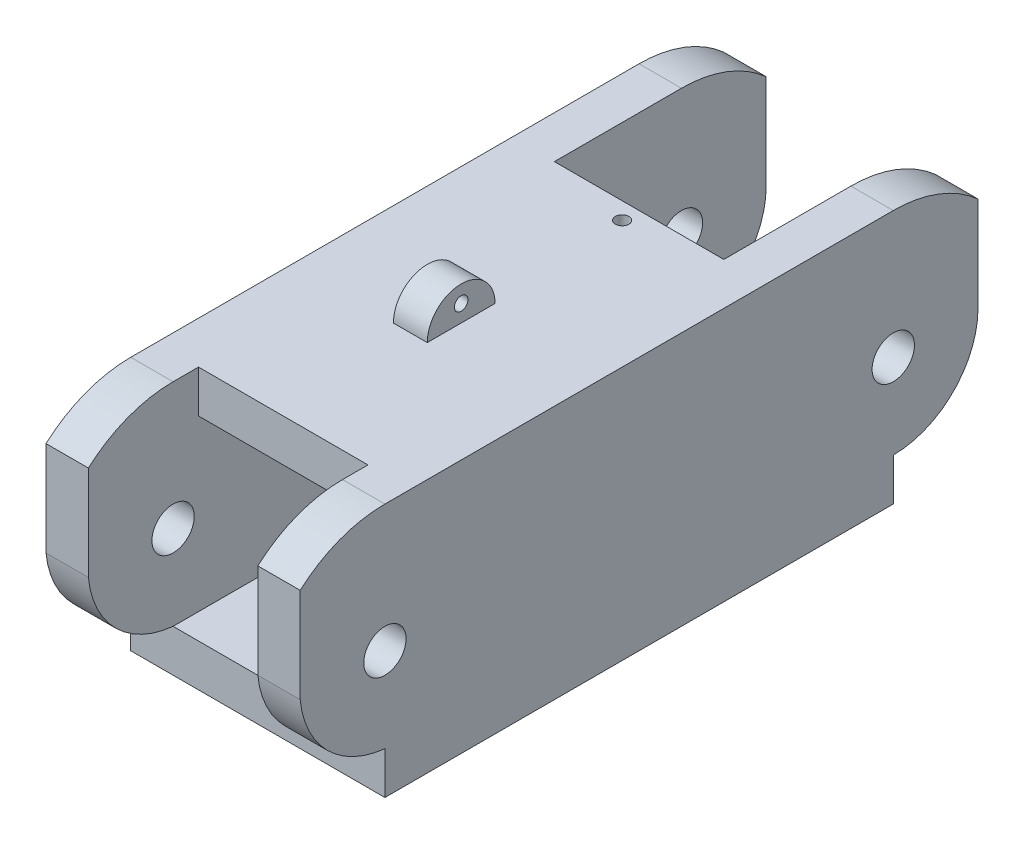
SolidWorks part; units mm, degrees
ref_plane "Front Plane" through (0, 0, 0) normal (0, 0, 1) x (1, 0, 0)
ref_plane "Top Plane" through (0, 0, 0) normal (0, 1, 0) x (1, 0, 0)
ref_plane "Right Plane" through (0, 0, 0) normal (1, 0, 0) x (0, 0, -1)
ref_plane "End Plane" through (0, 0, -31.75) normal (0, 0, 1) x (1, 0, 0)
ref_plane "Inside Plane" through (0, 19.05, 0) normal (0, 1, 0) x (1, 0, 0)
sketch "Sketch1" plane through (0, 0, 0) normal (0, 1, 0) x (1, 0, 0)
  line L1 (0, 0) -> (19.05, 0)
  line L2 (0, 0) -> (0, 57.15)
  line L3 (0, 57.15) -> (19.05, 57.15)
  line L4 (19.05, 0) -> (19.05, 57.15)
  dimension "D1" = 57.15
  dimension "D2" = 19.05
extrude "Boss-Extrude1" add sketch "Sketch1" along normal blind 19.05
sketch "Sketch2" plane through (0, 0, 0) normal (0, 0, 1) x (1, 0, 0)
  line L0 (0, 19.05) -> (19.05, 19.05) construction
  line L1 (3.175, 15.875) -> (15.875, 15.875)
  line L2 (3.175, 15.875) -> (3.175, 3.175)
  line L3 (3.175, 3.175) -> (15.875, 3.175)
  line L4 (15.875, 15.875) -> (15.875, 3.175)
  line L5 (0, 19.05) -> (0, 0) construction
  line L6 (0, 0) -> (19.05, 0) construction
  line L7 (19.05, 19.05) -> (19.05, 0) construction
  dimension "D1" = 3.175
  dimension "D2" = 3.175
  dimension "D3" = 3.175
  dimension "D4" = 3.175
extrude "Cut-Extrude1" cut sketch "Sketch2" against normal blind 76.2
sketch "Sketch3" plane through (0, 19.05, 0) normal (0, 1, 0) x (1, 0, 0)
  line L0 (0, 57.15) -> (0, 0) construction
  line L1 (7.62, 26.67) -> (10.16, 26.67)
  line L2 (7.62, 26.67) -> (7.62, 21.59)
  line L3 (7.62, 21.59) -> (10.16, 21.59)
  line L4 (10.16, 26.67) -> (10.16, 21.59)
  line L5 (0, 0) -> (19.05, 0) construction
  dimension "D1" = 2.54
  dimension "D2" = 7.62
  dimension "D3" = 21.59
  dimension "D4" = 5.08
extrude "Boss-Extrude2" add sketch "Sketch3" along normal blind 2.54
sketch "Sketch4" plane through (0, 0, 0) normal (1, 0, 0) x (0, 0, -1)
  line L0 (26.67, 19.05) -> (21.59, 19.05) construction
  line L1 (24.13, 21.59) -> (24.13, 20.32) construction
  line L2 (57.15, 19.05) -> (0, 19.05) construction
  line L3 (21.59, 21.59) -> (26.67, 21.59) construction
  line L4 (57.15, 0) -> (0, 0) construction
  line L5 (0, 19.05) -> (0, 0) construction
  circle A0 centre (24.13, 20.32) radius 0.508
  arc A1 (26.67, 19.05) -> (21.59, 19.05) centre (24.13, 21.3579) ccw
  circle A4 centre (9.525, 9.525) radius 1.5875
  arc A6 (9.525, 19.05) -> (9.525, 0) centre (9.525, 9.525) ccw
  arc A7 (9.525, 19.05) -> (9.525, 0) centre (-8.7829, 9.525) ccw
  ellipse E0 centre (24.13, 19.05) end of major axis (21.59, 19.05) minor radius 2.54 (26.67, 19.05) -> (21.59, 19.05) ccw
  dimension "D1" = 1.27
  dimension "D4" = 9.525
  dimension "D5" = 9.525
extrude "Cut-Extrude2" cut sketch "Sketch4" along normal blind 19.05
fillet "Fillet1" [suppressed] radius 0.635
fillet "Fillet2" [suppressed] radius 2.54
sketch "Sketch7" plane through (0, 19.05, 0) normal (0, 1, 0) x (1, 0, 0)
  line L2 (3.175, 0) -> (3.175, 11.43)
  line L3 (3.175, 11.43) -> (6.35, 11.43)
  line L6 (15.875, 0) -> (15.875, 11.43)
  line L7 (15.875, 11.43) -> (12.7, 11.43)
  line L10 (3.175, 0) -> (15.875, 0)
  line L11 (0, 57.15) -> (0, 9.525) construction
  line L12 (6.35, 11.43) -> (12.7, 11.43)
  line L13 (10.16, 26.67) -> (7.62, 26.67) construction
  circle A0 centre (9.525, 36.83) radius 0.508
  dimension "D5" = 9.525
  dimension "D1" = 3.175
  dimension "D2" = 3.175
  dimension "D3" = 11.43
  dimension "D4" = 11.43
  dimension "D6" = 10.16
extrude "Cut-Extrude3" cut sketch "Sketch7" against normal blind 12.7
sketch "Sketch8" plane through (0, 19.05, 0) normal (0, 1, 0) x (1, 0, 0)
  line L0 (3.175, 0) -> (3.175, 9.525) construction
  line L1 (3.175, 0) -> (15.875, 0)
  line L2 (3.175, 0) -> (3.175, 9.525)
  line L3 (3.175, 9.525) -> (15.875, 9.525)
  line L4 (15.875, 0) -> (15.875, 9.525)
extrude "Cut-Extrude4" cut sketch "Sketch8" against normal blind 25.4
sketch "Sketch9" plane through (0, 0, 0) normal (0, 1, 0) x (1, 0, 0)
  line L0 (3.175, 9.525) -> (15.875, 9.525) construction
  line L1 (12.065, 22.225) -> (8.255, 22.225)
  line L2 (12.065, 22.225) -> (12.065, 27.305)
  line L3 (12.065, 27.305) -> (8.255, 27.305)
  line L4 (8.255, 22.225) -> (8.255, 27.305)
  line L5 (19.05, 9.525) -> (19.05, 57.15) construction
  dimension "D1" = 3.81
  dimension "D2" = 5.08
  dimension "D3" = 12.7
  dimension "D4" = 6.985
extrude "Boss-Extrude3" [suppressed] add sketch "Sketch9" against normal blind 5.08
sketch "Sketch10" [suppressed] plane through (0, 0, 0) normal (1, 0, 0) x (0, 0, -1)
  line L0 (27.305, -5.08) -> (27.305, 0) construction
  line L1 (22.225, -5.08) -> (27.305, -5.08) construction
  line L2 (22.225, -5.08) -> (22.225, 0) construction
  line L3 (22.225, 0) -> (27.305, 0) construction
  line L4 (22.225, -2.54) -> (22.225, 0)
  line L5 (25.1652, 0) -> (27.305, 0)
  line L6 (9.525, 0) -> (41.275, 0) construction
  arc A0 (27.305, -2.54) -> (24.765, -5.08) centre (24.765, -2.54) cw
  arc A1 (24.765, -5.08) -> (22.225, -2.54) centre (24.765, -2.54) cw
  arc A2 (27.305, -2.54) -> (26.0285, -1.3339) centre (26.0637, -2.5752) ccw
  arc A3 (26.0285, -1.3339) -> (26.0483, -2.0347) centre (26.0384, -1.6843) ccw
  arc A4 (26.0483, -2.0347) -> (26.68, -2.5752) centre (26.0422, -2.6811) cw
  arc A5 (26.68, -2.5752) -> (24.765, -4.4612) centre (24.5539, -2.3316) cw
  arc A6 (24.765, -4.4612) -> (22.9012, -2.54) centre (25.0593, -2.311) cw
  arc A7 (22.9012, -2.54) -> (25.1652, 0) centre (27.0171, -3.9296) cw
  arc A8 (27.305, 0) -> (22.225, 0) centre (24.765, -2.8187) cw
extrude "Cut-Extrude5" [suppressed] cut sketch "Sketch10" along normal blind 25.4
sketch "Sketch11" plane through (0, 0, 0) normal (1, 0, 0) x (0, 0, -1)
  line L3 (9.525, 19.05) -> (57.15, 19.05) construction
  line L4 (9.525, 0) -> (57.15, 0) construction
  line L5 (57.15, 19.05) -> (57.15, 0) construction
  circle A0 centre (47.625, 9.525) radius 1.5875
  arc A1 (47.625, 0) -> (47.625, 19.05) centre (47.625, 9.525) ccw
  arc A2 (47.625, 19.05) -> (47.625, 0) centre (52.9788, 9.525) cw
extrude "Cut-Extrude6" cut sketch "Sketch11" along normal blind 19.05
sketch "Sketch12" plane through (0, 19.05, 0) normal (0, 1, 0) x (1, 0, 0)
  line L0 (19.05, 47.625) -> (0, 47.625) construction
  line L1 (3.175, 69.071) -> (15.875, 69.071)
  line L2 (3.175, 69.071) -> (3.175, 38.1)
  line L3 (3.175, 38.1) -> (15.875, 38.1)
  line L4 (15.875, 69.071) -> (15.875, 38.1)
  dimension "D1" = 9.525
extrude "Cut-Extrude7" cut sketch "Sketch12" against normal blind 3.81
sketch "Sketch13" plane through (0, 0, 0) normal (0, 1, 0) x (1, 0, 0)
  line L1 (3.175, 67.0881) -> (15.875, 67.0881)
  line L2 (3.175, 67.0881) -> (3.175, 47.625)
  line L3 (3.175, 47.625) -> (15.875, 47.625)
  line L4 (15.875, 67.0881) -> (15.875, 47.625)
extrude "Cut-Extrude8" cut sketch "Sketch13" along normal blind 3.81
sketch "Sketch14" plane through (0, 0, 0) normal (1, 0, 0) x (0, 0, -1)
  line L0 (9.525, 0) -> (9.525, 3.175)
  line L1 (3.175, 9.525) -> (3.175, 18.7413)
  line L2 (47.625, 0) -> (47.625, 3.175)
  line L3 (3.175, 18.7413) -> (-3.7286, 9.9787)
  line L4 (-3.7286, 9.9787) -> (-2.5445, 0)
  line L5 (-2.5445, 0) -> (9.525, 0)
  line L7 (53.975, 9.525) -> (53.975, 20.2011)
  line L8 (53.975, 20.2011) -> (59.4227, 9.525)
  line L9 (59.4227, 9.525) -> (58.0629, -0.3326)
  line L10 (58.0629, -0.3326) -> (47.625, 0)
  arc A1 (3.175, 9.525) -> (9.525, 3.175) centre (10.2236, 10.2236) ccw
  arc A2 (47.625, 3.175) -> (53.975, 9.525) centre (47.625, 9.525) ccw
  arc A3 (9.525, 19.05) -> (9.525, 0) centre (9.525, 9.525) ccw construction
  arc A5 (47.625, 0) -> (47.625, 19.05) centre (47.625, 9.525) ccw construction
  point P7 (0, 9.525)
  point P19 (57.15, 9.525)
  dimension "D2" = 3.175
  dimension "D5" = 6.35
  dimension "D1" = 3.175
  dimension "D3" = 3.175
  dimension "D4" = 3.175
extrude "Cut-Extrude9" cut sketch "Sketch14" along normal blind 19.05
